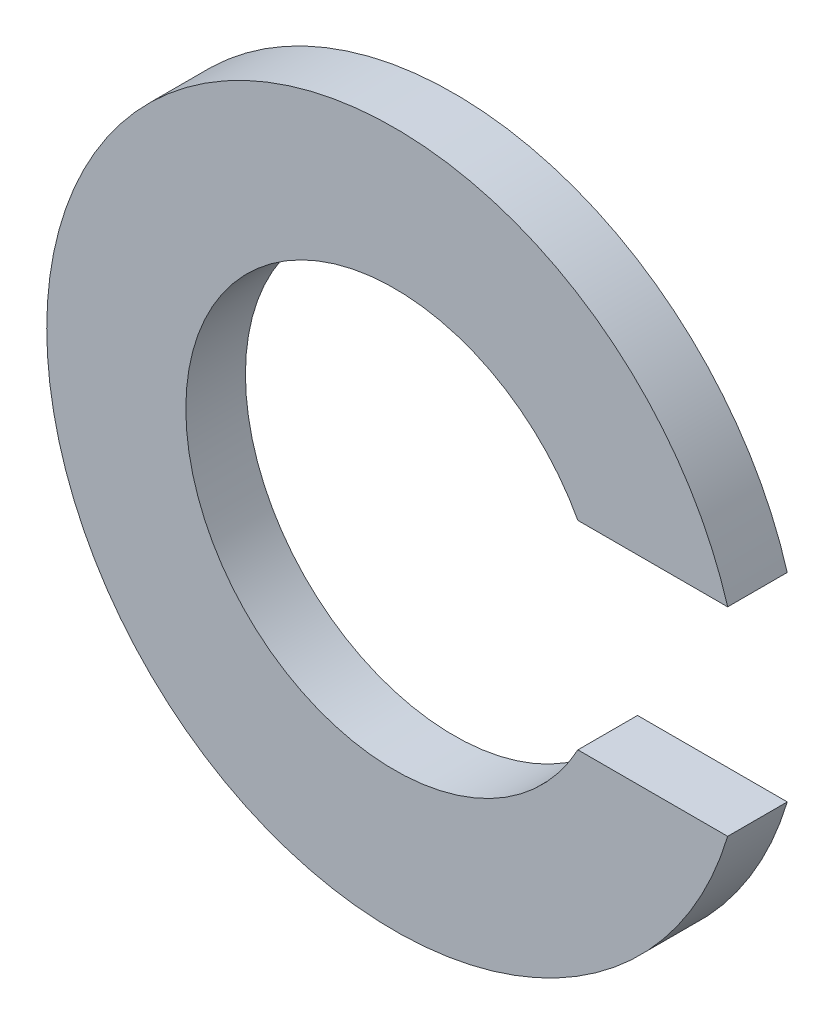
SolidWorks part; units mm, degrees
ref_plane "Front Plane" through (0, 0, 0) normal (0, 0, 1) x (1, 0, 0)
ref_plane "Top Plane" through (0, 0, 0) normal (0, 1, 0) x (1, 0, 0)
ref_plane "Right Plane" through (0, 0, 0) normal (1, 0, 0) x (0, 0, -1)
sketch "Sketch1" plane through (0, 0, 0) normal (0, 0, 1) x (1, 0, 0)
  line L0 (1.8466, 1) -> (3.3541, 1)
  line L1 (1.8466, -1) -> (3.3541, -1)
  line L2 (0, 0) -> (3, 0) construction
  arc A0 (1.8466, 1) -> (1.8466, -1) centre (0, 0) ccw
  arc A1 (3.3541, 1) -> (3.3541, -1) centre (0, 0) ccw
  dimension "D1" = 7
  dimension "D2" = 4.2
  dimension "D3" = 2
extrude "Boss-Extrude1" add sketch "Sketch1" along normal blind 0.6
